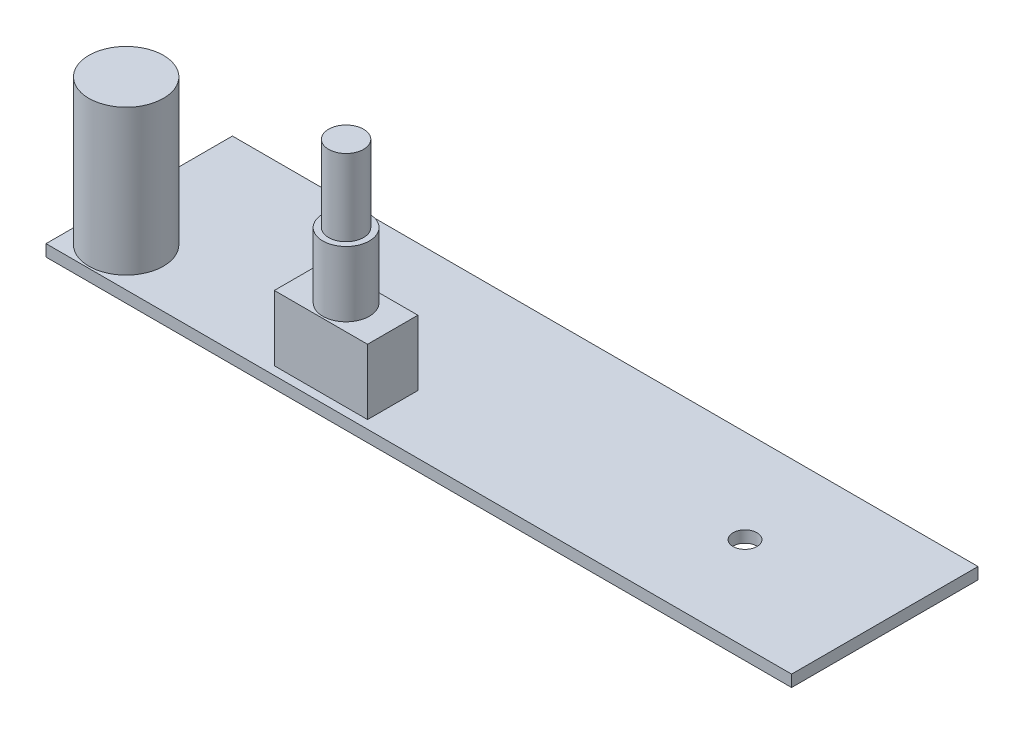
SolidWorks part; units mm, degrees
ref_plane "Front Plane" through (0, 0, 0) normal (0, 0, 1) x (1, 0, 0)
ref_plane "Top Plane" through (0, 0, 0) normal (0, 1, 0) x (1, 0, 0)
ref_plane "Right Plane" through (0, 0, 0) normal (1, 0, 0) x (0, 0, -1)
sketch "Sketch1" plane through (0, 0, 0) normal (0, 1, 0) x (1, 0, 0)
  line L1 (0, 0) -> (101.6, 0)
  line L2 (0, 0) -> (0, 25.4)
  line L3 (0, 25.4) -> (101.6, 25.4)
  line L4 (101.6, 0) -> (101.6, 25.4)
  dimension "D1" = 101.6
  dimension "D2" = 25.4
extrude "Boss-Extrude1" add sketch "Sketch1" along normal blind 1.5875
hole_wizard "#4 Clearance Hole2" positions "Sketch4" profile "Sketch3" hole size "#4" standard "ANSI Inch" end condition up to next
sketch "Sketch4" plane through (0, 1.5875, 0) normal (0, 1, 0) x (1, 0, 0)
  line L1 (31.75, 12.7) -> (82.55, 12.7)
  line L3 (101.6, 0) -> (101.6, 25.4) construction
  point P0 (31.75, 12.7)
  point P2 (82.55, 12.7)
  point P13 (101.6, 12.7)
  dimension "D1" = 19.05
  dimension "D2" = 69.85
sketch "Sketch3" plane through (31.75, 1.5875, -12.7) normal (1, 0, 0) x (0, 0, 1)
  line L0 (0, 0) -> (0, 1.5875)
  line L1 (0, 1.5875) -> (1.6319, 1.5875)
  line L2 (1.6319, 1.5875) -> (1.6319, 0)
  line L5 (1.6319, 0) -> (0, 0)
  line L11 (0, -6.35) -> (0, 107.95) construction
  dimension "Thru Hole Dia." = 3.2639
  dimension "Thru Hole Depth" = 1.5875
sketch "Sketch5" plane through (0, 1.5875, 0) normal (0, 1, 0) x (1, 0, 0)
  line L0 (101.6, 25.4) -> (0, 25.4) construction
  line L1 (101.6, 0) -> (101.6, 25.4) construction
  circle A0 centre (5.588, 5.334) radius 5.08
  dimension "D1" = 20.066
  dimension "D3" = 10.16
  dimension "D2" = 96.012
extrude "Boss-Extrude2" add sketch "Sketch5" along normal blind 19.812
sketch "Sketch6" plane through (0, 1.5875, 0) normal (0, 1, 0) x (1, 0, 0)
  line L0 (101.6, 0) -> (101.6, 25.4) construction
  line L1 (42.672, 8.001) -> (29.972, 8.001)
  line L2 (42.672, 8.001) -> (42.672, 1.143)
  line L3 (42.672, 1.143) -> (29.972, 1.143)
  line L4 (29.972, 8.001) -> (29.972, 1.143)
  line L5 (42.672, 8.001) -> (29.972, 1.143) construction
  line L6 (42.672, 1.143) -> (29.972, 8.001) construction
  line L7 (101.6, 25.4) -> (0, 25.4) construction
  point P0 (36.322, 4.572)
  dimension "D1" = 65.278
  dimension "D2" = 20.828
  dimension "D3" = 6.858
  dimension "D4" = 12.7
extrude "Boss-Extrude3" add sketch "Sketch6" along normal blind 8.89
sketch "Sketch7" plane through (0, 10.4775, 0) normal (0, 1, 0) x (1, 0, 0)
  line L0 (36.322, 1.143) -> (36.322, 8.001) construction
  line L4 (29.972, 8.001) -> (29.972, 1.143)
  line L5 (29.972, 1.143) -> (42.672, 1.143)
  line L6 (42.672, 1.143) -> (42.672, 8.001)
  line L7 (42.672, 8.001) -> (29.972, 8.001)
  line L8 (29.972, 8.001) -> (29.972, 1.143)
  line L9 (29.972, 1.143) -> (42.672, 1.143)
  line L10 (42.672, 1.143) -> (42.672, 8.001)
  line L11 (42.672, 8.001) -> (29.972, 8.001)
  circle A0 centre (36.322, 4.572) radius 3.175
  dimension "D2" = 6.35
  dimension "D1" = 0
extrude "Boss-Extrude4" add sketch "Sketch7" along normal blind 8.89 contours L0 A0 | A0 L0
sketch "Sketch8" plane through (0, 19.3675, 0) normal (0, 1, 0) x (1, 0, 0)
  circle A0 centre (36.322, 4.572) radius 2.3812
  dimension "D1" = 4.7625
extrude "Boss-Extrude5" add sketch "Sketch8" along normal blind 10.414
sketch "Sketch11" plane through (0, 1.5875, 0) normal (0, 1, 0) x (1, 0, 0)
  line L0 (101.6, 12.7) -> (0, 12.7) construction
  line L1 (57.912, 22.098) -> (91.44, 22.098)
  line L2 (57.912, 22.098) -> (57.912, 3.302)
  line L3 (57.912, 3.302) -> (91.44, 3.302)
  line L4 (91.44, 22.098) -> (91.44, 3.302)
  line L5 (57.912, 22.098) -> (91.44, 3.302) construction
  line L6 (57.912, 3.302) -> (91.44, 22.098) construction
  line L7 (101.6, 0) -> (101.6, 25.4) construction
  line L8 (0, 25.4) -> (0, 0) construction
  point P0 (74.676, 12.7)
  dimension "D1" = 18.796
  dimension "D2" = 33.528
  dimension "D3" = 10.16
sketch "Sketch12" plane through (0, 1.5875, 0) normal (0, 1, 0) x (1, 0, 0)
  line L0 (91.44, 22.098) -> (91.44, 3.302) construction
  line L1 (57.912, 22.098) -> (91.44, 22.098) construction
  line L2 (57.912, 22.098) -> (57.912, 3.302) construction
  line L3 (57.912, 3.302) -> (91.44, 3.302) construction
  line L4 (91.44, 22.098) -> (91.44, 3.302)
  line L5 (57.912, 22.098) -> (91.44, 22.098)
  line L6 (57.912, 22.098) -> (57.912, 3.302)
  line L7 (57.912, 3.302) -> (91.44, 3.302)
